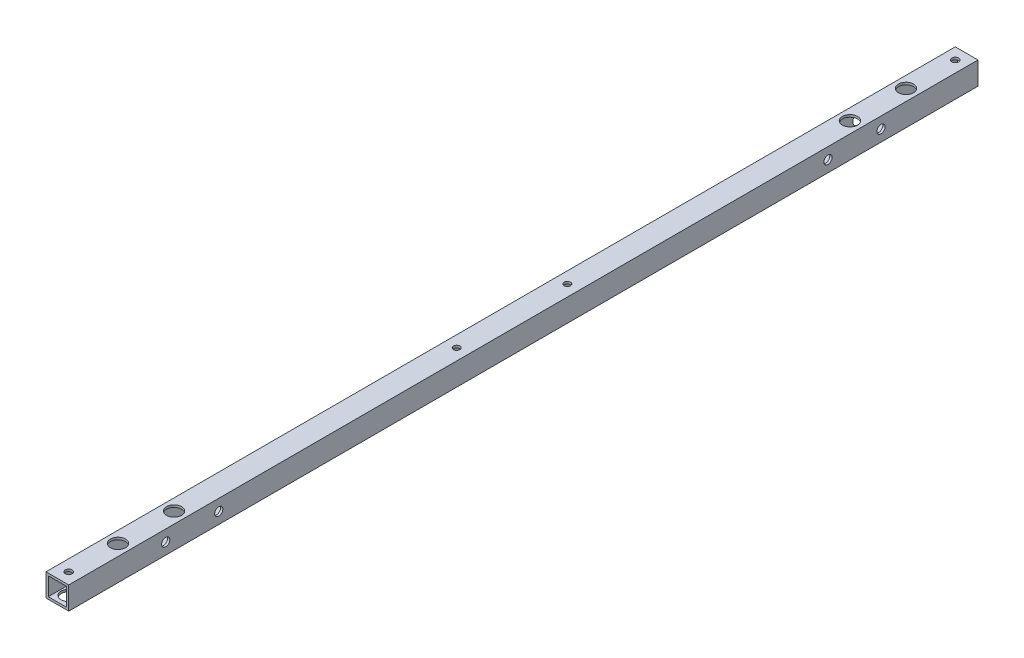
SolidWorks part; units mm, degrees
material "6063-T5"
ref_plane "正面" through (0, 0, 0) normal (0, 0, 1) x (1, 0, 0)
ref_plane "平面" through (0, 0, 0) normal (0, 1, 0) x (1, 0, 0)
ref_plane "右側面" through (0, 0, 0) normal (1, 0, 0) x (0, 0, -1)
sketch "ｽｹｯﾁ1" plane through (0, 0, 0) normal (0, 0, 1) x (1, 0, 0)
  line L1 (-7.5, -7.5) -> (7.5, -7.5)
  line L2 (-7.5, -7.5) -> (-7.5, 7.5)
  line L3 (-7.5, 7.5) -> (7.5, 7.5)
  line L4 (7.5, -7.5) -> (7.5, 7.5)
  line L5 (-7.5, -7.5) -> (7.5, 7.5) construction
  line L6 (-7.5, 7.5) -> (7.5, -7.5) construction
  line L7 (-6, -6) -> (6, -6)
  line L8 (-6, -6) -> (-6, 6)
  line L9 (-6, 6) -> (6, 6)
  line L10 (6, -6) -> (6, 6)
  line L11 (-6, -6) -> (6, 6) construction
  line L12 (-6, 6) -> (6, -6) construction
  point P0 (0, 0)
  point P6 (0, 0)
  dimension "D1" = 1.5
  dimension "D2" = 15
  dimension "D3" = 15
extrude "ﾎﾞｽ - 押し出し1" add sketch "ｽｹｯﾁ1" along normal blind 600
sketch "ｽｹｯﾁ3" plane through (0, 7.5, 0) normal (0, 1, 0) x (1, 0, 0)
  line L2 (7.5, -600) -> (7.5, 0) construction
  line L3 (7.5, 0) -> (-7.5, 0) construction
  circle A1 centre (0, -7.5) radius 2.25
  circle A6 centre (0, -592.5) radius 2.25
  dimension "D2" = 7.5
  dimension "D3" = 4.5
  dimension "D9" = 7.5
  dimension "D11" = 7.5
  dimension "D4" = 7.5
  dimension "D5" = 4.5
extrude "ｶｯﾄ - 押し出し2" cut sketch "ｽｹｯﾁ3" against normal blind 25
sketch "ｽｹｯﾁ4" plane through (7.5, 0, 0) normal (1, 0, 0) x (0, 0, -1)
  line L0 (-600, -7.5) -> (-600, 7.5) construction
  line L1 (-600, -7.5) -> (0, -7.5) construction
  line L2 (0, -7.5) -> (0, 7.5) construction
  circle A0 centre (-536, 0) radius 2.7
  circle A1 centre (-501, 0) radius 2.7
  circle A2 centre (-99, 0) radius 2.7
  circle A3 centre (-64, 0) radius 2.7
  dimension "D2" = 7.5
  dimension "D3" = 5.4
  dimension "D5" = 35
  dimension "D7" = 64
  dimension "D1" = 64
  dimension "D4" = 2
  dimension "D6" = 2
extrude "ｶｯﾄ - 押し出し3" cut sketch "ｽｹｯﾁ4" against normal blind 20
sketch "ｽｹｯﾁ6" plane through (0, 7.5, 0) normal (0, 1, 0) x (1, 0, 0)
  line L0 (-7.5, -600) -> (-7.5, 0) construction
  line L1 (7.5, -600) -> (7.5, 0) construction
  circle A0 centre (0, -336.5) radius 2.1
  circle A1 centre (0, -263.5) radius 2.1
  point P6 (-7.5, -300)
  dimension "D2" = 73
  dimension "D3" = 7.5
  dimension "D4" = 7.5
  dimension "D5" = 4.2
  dimension "D6" = 4.2
  dimension "D1" = 36.5
extrude "ｶｯﾄ - 押し出し4" cut sketch "ｽｹｯﾁ6" against normal blind 20
sketch "ｽｹｯﾁ9" plane through (0, -7.5, 0) normal (0, -1, 0) x (1, 0, 0)
  circle A0 centre (0, 592.5) radius 5
  circle A1 centre (0, 336.5) radius 5
  circle A2 centre (0, 263.5) radius 5
  circle A3 centre (0, 7.5) radius 5
  dimension "D1" = 10
  dimension "D2" = 10
  dimension "D3" = 10
  dimension "D4" = 10
extrude "ｶｯﾄ - 押し出し7" cut sketch "ｽｹｯﾁ9" against normal blind 10
sketch "ｽｹｯﾁ10" plane through (0, -7.5, 0) normal (0, -1, 0) x (-1, 0, 0)
  line L0 (7.5, 0) -> (-7.5, 0) construction
  line L1 (-7.5, -600) -> (-7.5, 0) construction
  line L2 (7.5, -600) -> (-7.5, -600) construction
  circle A0 centre (0, -40) radius 2.7
  circle A1 centre (0, -77) radius 2.7
  circle A2 centre (0, -523) radius 2.7
  circle A3 centre (0, -560) radius 2.7
  dimension "D1" = 37
  dimension "D2" = 40
  dimension "D3" = 7.5
  dimension "D5" = 5.4
  dimension "D6" = 5.4
  dimension "D8" = 40
  dimension "D4" = 7.5
  dimension "D7" = 2
extrude "ｶｯﾄ - 押し出し8" cut sketch "ｽｹｯﾁ10" against normal blind 30
sketch "ｽｹｯﾁ11" plane through (0, 7.5, 0) normal (0, 1, 0) x (1, 0, 0)
  circle A0 centre (0, -40) radius 5
  circle A1 centre (0, -77) radius 5
  circle A2 centre (0, -560) radius 5
  circle A3 centre (0, -523) radius 5
  point P12 (0, -40)
  point P14 (0, -523)
  dimension "D1" = 10
  dimension "D2" = 10
  dimension "D3" = 10
  dimension "D4" = 10
extrude "ｶｯﾄ - 押し出し9" cut sketch "ｽｹｯﾁ11" against normal blind 10
hole_wizard "Ø10.0 (10) 直径の穴1" positions "ｽｹｯﾁ12" profile "ｽｹｯﾁ14" hole size "Ø10.0" standard "JIS"
sketch "ｽｹｯﾁ12" plane through (-7.5, 0, 0) normal (-1, 0, 0) x (0, 0, 1)
  point P0 (64, 0)
  point P3 (99, 0)
  point P6 (501, 0)
  point P9 (536, 0)
sketch "ｽｹｯﾁ14" plane through (-7.5, 0, 64) normal (0, 1, 0) x (0, 0, 1)
  line L0 (0, 0) -> (0, 1.5)
  line L1 (0, 1.5) -> (5, 1.5)
  line L2 (5, 1.5) -> (5, 0)
  line L5 (5, 0) -> (0, 0)
  line L10 (0, 1.5) -> (-5, 1.5) construction
  line L11 (0, -6.35) -> (0, 107.95) construction
  dimension "穴の直径" = 10
  dimension "穴の深さ" = 1.5
  dimension "ﾄﾞﾘﾙ角度" = 180
